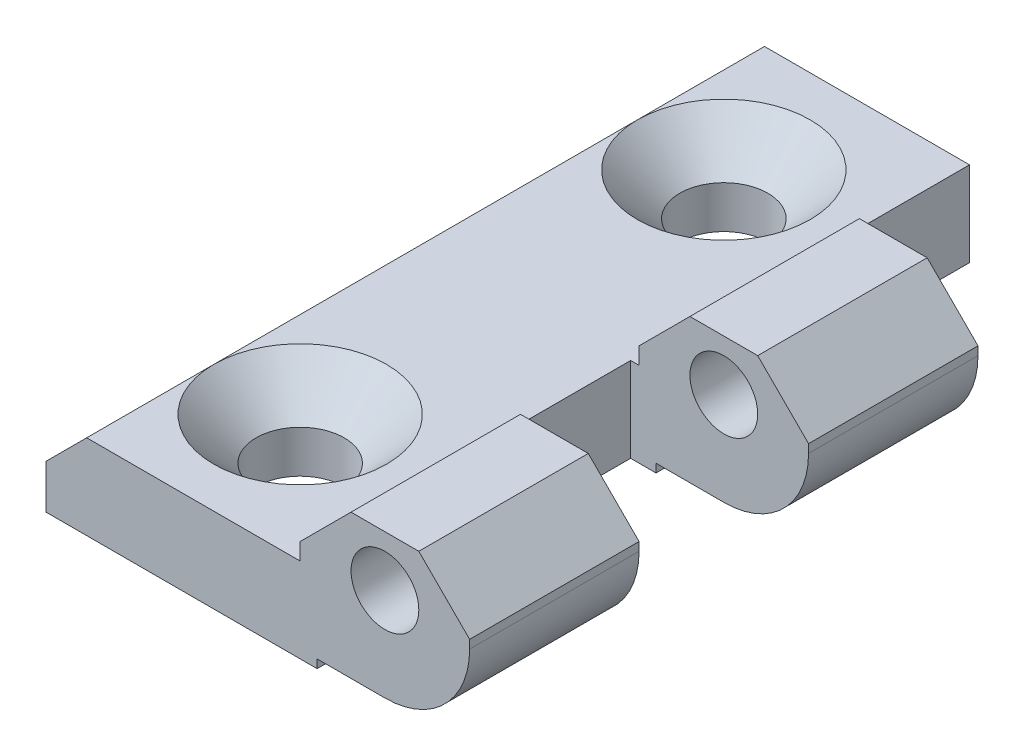
SolidWorks part; units mm, degrees
ref_plane "Front Plane" through (0, 0, 0) normal (0, 0, 1) x (1, 0, 0)
ref_plane "Top Plane" through (0, 0, 0) normal (0, 1, 0) x (1, 0, 0)
ref_plane "Right Plane" through (0, 0, 0) normal (1, 0, 0) x (0, 0, -1)
sketch "Sketch1" plane through (0, 0, 0) normal (0, 0, 1) x (1, 0, 0)
  line L0 (-31.4752, -9.9967) -> (-15.4752, -9.9967)
  line L1 (-15.4752, -9.9967) -> (-15.4752, -9.4967)
  line L2 (-15.4752, -9.4967) -> (-11.4752, -9.4967)
  line L3 (-6.4752, -4.4967) -> (-6.4752, -3.9967)
  line L4 (-6.4752, -3.9967) -> (-9.4752, -0.9967)
  line L5 (-9.4752, -0.9967) -> (-13.4752, -0.9967)
  line L6 (-13.4752, -0.9967) -> (-16.4752, -3.9967)
  line L7 (-16.4752, -3.9967) -> (-16.4752, -4.9967)
  line L8 (-16.4752, -4.9967) -> (-29.0752, -4.9967)
  line L9 (-29.0752, -4.9967) -> (-31.4752, -7.3967)
  line L10 (-31.4752, -7.3967) -> (-31.4752, -9.9967)
  arc A0 (-11.4752, -9.4967) -> (-6.4752, -4.4967) centre (-11.4752, -4.4967) ccw
  circle A1 centre (-11.4752, -3.9967) radius 2
extrude "Extrude1" add sketch "Sketch1" along normal blind 40
sketch "Sketch2" plane through (0, -4.9967, 0) normal (0, 1, 0) x (1, 0, 0)
  line L0 (-9.4752, -20) -> (-16.9752, -20)
  line L1 (-9.4752, -40) -> (-13.4752, -40) construction
  line L3 (-16.9752, -28.7001) -> (-16.9752, -20)
  line L7 (-9.4752, -10) -> (-16.9752, -10)
  line L11 (-9.4752, 0) -> (-16.9752, 0)
  line L13 (-9.4752, -20) -> (-3.0731, -20)
  line L14 (-3.0731, -20) -> (-3.0731, -30)
  line L15 (-3.0731, -30) -> (-16.9752, -30)
  line L16 (-16.9752, -30) -> (-16.9752, -28.7001)
  line L17 (-9.4752, 0) -> (-4.9097, 0)
  line L18 (-4.9097, 0) -> (-4.9097, -10)
  line L19 (-4.9097, -10) -> (-9.4752, -10)
  line L20 (-16.9752, -10) -> (-16.9752, 0)
  dimension "D1" = 10
  dimension "D2" = 10
  dimension "D3" = 10
  dimension "D4" = 10
extrude "Cut-Extrude1" cut sketch "Sketch2" against normal through all and the other way through all
sketch "Sketch3" plane through (0, -4.9967, 0) normal (0, 1, 0) x (1, 0, 0)
  line L5 (-11.4752, -7.5) -> (-23.9752, -7.5)
  line L6 (-11.4752, -32.5) -> (-23.9752, -32.5)
hole_wizard "Hole1" positions "3DSketch1" profile "Sketch4" legacy end condition through all
sketch3d "3DSketch1"
  point P0 (-23.9752, -4.9967, 7.5)
  point P2 (-23.9752, -4.9967, 32.5)
sketch "Sketch4" plane through (-23.9752, -4.9967, 7.5) normal (1, 0, 0) x (0, 0, 1)
  line L0 (0, 0) -> (0, 5)
  line L1 (0, 5) -> (2.6, 5)
  line L2 (2.6, 5) -> (2.6, 2.5)
  line L3 (2.6, 2.5) -> (5.1, 0)
  line L5 (5.1, 0) -> (0, 0)
  line L6 (-2.6, 2.5) -> (-5.1, 0) construction
  line L11 (0, -6.35) -> (0, 107.95) construction
  dimension "Thru Hole Dia." = 5.2
  dimension "Thru Hole Depth" = 5
  dimension "Near C'Sink Dia." = 10.2
  dimension "Near C'Sink Angle" = 90
